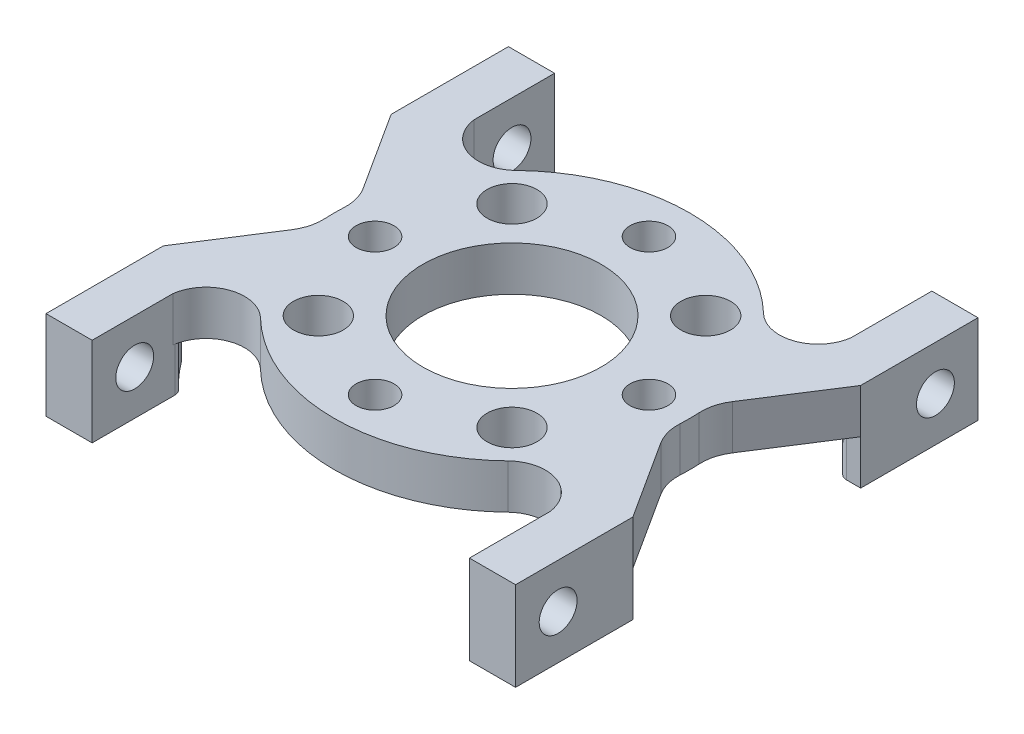
SolidWorks part; units mm, degrees
ref_plane "Front Plane" through (0, 0, 0) normal (0, 0, 1) x (1, 0, 0)
ref_plane "Top Plane" through (0, 0, 0) normal (0, 1, 0) x (1, 0, 0)
ref_plane "Right Plane" through (0, 0, 0) normal (1, 0, 0) x (0, 0, -1)
ref_plane "Plane1" through (0, 0, 0) normal (0, -1, 0) x (1, 0, 0)
sketch "Sketch1" plane through (0, 0, 0) normal (0, -1, 0) x (1, 0, 0)
  line L0 (16.764, 16.51) -> (-16.764, 16.51)
  line L1 (-16.764, 16.51) -> (-16.764, -16.51)
  line L2 (-16.764, -16.51) -> (16.764, -16.51)
  line L3 (16.764, -16.51) -> (16.764, 16.51)
extrude "Boss-Extrude1" add sketch "Sketch1" against normal blind 3.175
sketch "Sketch2" plane through (0, 3.175, 0) normal (0, 1, 0) x (-1, 0, 0)
  line L0 (-13.4696, 16.51) -> (-13.4696, 10.7533)
  line L1 (13.4696, 10.7533) -> (13.4696, 16.51)
  line L2 (13.4696, 16.51) -> (-13.4696, 16.51)
  arc A0 (-13.4696, 10.7533) -> (-8.8308, 9.1273) centre (-10.7425, 11.1033) ccw
  arc A1 (-8.8308, 9.1273) -> (8.8308, 9.1273) centre (0, 0) cw
  arc A2 (8.8308, 9.1273) -> (13.4696, 10.7533) centre (10.7425, 11.1033) ccw
extrude "Cut-Extrude1" cut sketch "Sketch2" against normal through all
sketch "Sketch3" plane through (0, 0, 0) normal (0, -1, 0) x (1, 0, 0)
  line L0 (-13.4696, 8.1331) -> (-16.764, 8.1331)
  line L1 (-16.764, 8.1331) -> (-16.764, 16.51)
  line L2 (-16.764, 16.51) -> (-13.4696, 16.51)
  line L3 (-13.4696, 16.51) -> (-13.4696, 8.1331)
extrude "Boss-Extrude2" add sketch "Sketch3" along normal blind 3.175
sketch "Sketch4" plane through (0, 3.175, 0) normal (0, 1, 0) x (-1, 0, 0)
  line L0 (-16.764, 8.1331) -> (-16.764, -8.1331)
  line L1 (-16.764, -8.1331) -> (-12.5937, -1.6399)
  line L2 (-12.5937, 1.6399) -> (-16.764, 8.1331)
  arc A0 (-12.5937, -1.6399) -> (-12.5937, 1.6399) centre (0, 0) cw
extrude "Cut-Extrude2" cut sketch "Sketch4" against normal through all
sketch "Sketch5" plane through (0, 0, 0) normal (0, -1, 0) x (1, 0, 0)
  line L0 (13.4696, 8.1331) -> (13.4696, 16.51)
  line L1 (13.4696, 16.51) -> (16.764, 16.51)
  line L2 (16.764, 16.51) -> (16.764, 8.1331)
  line L3 (16.764, 8.1331) -> (13.4696, 8.1331)
extrude "Boss-Extrude3" add sketch "Sketch5" along normal blind 3.175
sketch "Sketch6" plane through (0, 3.175, 0) normal (0, 1, 0) x (-1, 0, 0)
  line L0 (13.4696, -16.51) -> (13.4696, -10.7533)
  line L1 (-13.4696, -10.7533) -> (-13.4696, -16.51)
  line L2 (-13.4696, -16.51) -> (13.4696, -16.51)
  arc A0 (13.4696, -10.7533) -> (8.8308, -9.1273) centre (10.7425, -11.1033) ccw
  arc A1 (8.8308, -9.1273) -> (-8.8308, -9.1273) centre (0, 0) cw
  arc A2 (-8.8308, -9.1273) -> (-13.4696, -10.7533) centre (-10.7425, -11.1033) ccw
extrude "Cut-Extrude3" cut sketch "Sketch6" against normal through all
sketch "Sketch7" plane through (0, 0, 0) normal (0, -1, 0) x (1, 0, 0)
  line L0 (13.4696, -8.1331) -> (16.764, -8.1331)
  line L1 (16.764, -8.1331) -> (16.764, -16.51)
  line L2 (16.764, -16.51) -> (13.4696, -16.51)
  line L3 (13.4696, -16.51) -> (13.4696, -8.1331)
extrude "Boss-Extrude4" add sketch "Sketch7" along normal blind 3.175
sketch "Sketch8" plane through (0, 3.175, 0) normal (0, 1, 0) x (-1, 0, 0)
  line L0 (16.764, -8.1331) -> (16.764, 8.1331)
  line L1 (16.764, 8.1331) -> (12.5937, 1.6399)
  line L2 (12.5937, -1.6399) -> (16.764, -8.1331)
  arc A0 (12.5937, 1.6399) -> (12.5937, -1.6399) centre (0, 0) cw
extrude "Cut-Extrude4" cut sketch "Sketch8" against normal through all
sketch "Sketch9" plane through (0, 0, 0) normal (0, -1, 0) x (1, 0, 0)
  line L0 (-13.4696, -8.1331) -> (-13.4696, -16.51)
  line L1 (-13.4696, -16.51) -> (-16.764, -16.51)
  line L2 (-16.764, -16.51) -> (-16.764, -8.1331)
  line L3 (-16.764, -8.1331) -> (-13.4696, -8.1331)
extrude "Boss-Extrude5" add sketch "Sketch9" along normal blind 3.175
sketch "Sketch10" plane through (0, -3.175, 0) normal (0, -1, 0) x (1, 0, 0)
  line L0 (15.4224, -8.1331) -> (13.4696, -8.1331)
  line L1 (13.4696, -8.1331) -> (13.4696, -10.3293)
  arc A0 (13.4696, -10.3293) -> (15.4224, -8.1331) centre (4.064, 0) ccw
extrude "Cut-Extrude5" cut sketch "Sketch10" against normal blind 3.175
sketch "Sketch11" plane through (0, -3.175, 0) normal (0, -1, 0) x (1, 0, 0)
  line L0 (13.4696, 10.3293) -> (13.4696, 8.1331)
  line L1 (13.4696, 8.1331) -> (15.4224, 8.1331)
  arc A0 (15.4224, 8.1331) -> (13.4696, 10.3293) centre (4.064, 0) ccw
extrude "Cut-Extrude6" cut sketch "Sketch11" against normal blind 3.175
sketch "Sketch12" plane through (0, -3.175, 0) normal (0, -1, 0) x (1, 0, 0)
  line L0 (-15.4224, 8.1331) -> (-13.4696, 8.1331)
  line L1 (-13.4696, 8.1331) -> (-13.4696, 10.3293)
  arc A0 (-13.4696, 10.3293) -> (-15.4224, 8.1331) centre (-4.064, 0) ccw
extrude "Cut-Extrude7" cut sketch "Sketch12" against normal blind 3.175
sketch "Sketch13" plane through (0, -3.175, 0) normal (0, -1, 0) x (1, 0, 0)
  line L0 (-13.4696, -10.3293) -> (-13.4696, -8.1331)
  line L1 (-13.4696, -8.1331) -> (-15.4224, -8.1331)
  arc A0 (-15.4224, -8.1331) -> (-13.4696, -10.3293) centre (-4.064, 0) ccw
extrude "Cut-Extrude8" cut sketch "Sketch13" against normal blind 3.175
hole_wizard "Hole1" positions "Sketch15" profile "Sketch14" legacy
sketch "Sketch15" plane through (0, 0, 0) normal (0, -1, 0) x (-1, 0, 0)
  point P0 (0, 0)
sketch "Sketch14" plane through (0, 0, 0) normal (1, 0, 0) x (0, 0, -1)
  line L0 (0, 0) -> (0, 3.175)
  line L1 (0, 3.175) -> (6.3627, 3.175)
  line L2 (6.3627, 3.175) -> (6.3627, 0)
  line L3 (6.3627, 0) -> (0, 0)
  line L4 (0, 110) -> (0, -10) construction
  dimension "Diameter" = 12.7254
  dimension "Depth" = 3.175
hole_wizard "M2.5 Clearance Hole1" positions "Sketch17" profile "Sketch16" hole size "M2.5" standard "ANSI Metric"
sketch "Sketch17" plane through (0, 0, 0) normal (0, -1, 0) x (-1, 0, 0)
  point P0 (0, -9.779)
  point P1 (9.779, 0)
  point P2 (0, 9.779)
  point P3 (-9.779, 0)
sketch "Sketch16" plane through (0, 0, 9.779) normal (1, 0, 0) x (0, 0, -1)
  line L0 (0, 0) -> (0, 3.175)
  line L1 (0, 3.175) -> (1.3525, 3.175)
  line L2 (1.3525, 3.175) -> (1.3525, 0)
  line L5 (1.3525, 0) -> (0, 0)
  line L11 (0, -6.35) -> (0, 107.95) construction
  dimension "Thru Hole Dia." = 2.7051
  dimension "Thru Hole Depth" = 3.175
hole_wizard "M3 Clearance Hole1" positions "Sketch19" profile "Sketch18" hole size "M3" standard "ANSI Metric"
sketch "Sketch19" plane through (0, 0, 0) normal (0, -1, 0) x (-1, 0, 0)
  point P0 (6.9148, -6.9148)
  point P1 (6.9148, 6.9148)
  point P2 (-6.9148, 6.9148)
  point P3 (-6.9148, -6.9148)
sketch "Sketch18" plane through (-6.9148, 0, 6.9148) normal (1, 0, 0) x (0, 0, -1)
  line L0 (0, 0) -> (0, 3.175)
  line L1 (0, 3.175) -> (1.778, 3.175)
  line L2 (1.778, 3.175) -> (1.778, 0)
  line L5 (1.778, 0) -> (0, 0)
  line L11 (0, -6.35) -> (0, 107.95) construction
  dimension "Thru Hole Dia." = 3.556
  dimension "Thru Hole Depth" = 3.175
hole_wizard "M2.5 Clearance Hole2" positions "Sketch21" profile "Sketch20" hole size "M2.5" standard "ANSI Metric"
sketch "Sketch21" plane through (16.764, 0, 0) normal (1, 0, 0) x (0, 0, -1)
  point P0 (13.4704, 0)
sketch "Sketch20" plane through (16.764, 0, -13.4704) normal (0, 1, 0) x (0, 0, -1)
  line L0 (0, 0) -> (0, 3.2944)
  line L1 (0, 3.2944) -> (1.3525, 3.2944)
  line L2 (1.3525, 3.2944) -> (1.3525, 0)
  line L5 (1.3525, 0) -> (0, 0)
  line L11 (0, -6.35) -> (0, 107.95) construction
  dimension "Thru Hole Dia." = 2.7051
  dimension "Thru Hole Depth" = 3.2944
hole_wizard "M2.5 Clearance Hole3" positions "Sketch23" profile "Sketch22" hole size "M2.5" standard "ANSI Metric"
sketch "Sketch23" plane through (13.4696, 0, 0) normal (-1, 0, 0) x (0, 0, 1)
  point P0 (13.4704, 0)
sketch "Sketch22" plane through (13.4696, 0, 13.4704) normal (0, 1, 0) x (0, 0, 1)
  line L0 (0, 0) -> (0, 3.2944)
  line L1 (0, 3.2944) -> (1.3525, 3.2944)
  line L2 (1.3525, 3.2944) -> (1.3525, 0)
  line L5 (1.3525, 0) -> (0, 0)
  line L11 (0, -6.35) -> (0, 107.95) construction
  dimension "Thru Hole Dia." = 2.7051
  dimension "Thru Hole Depth" = 3.2944
hole_wizard "M2.5 Clearance Hole4" positions "Sketch25" profile "Sketch24" hole size "M2.5" standard "ANSI Metric"
sketch "Sketch25" plane through (-13.4696, 0, 0) normal (1, 0, 0) x (0, 0, -1)
  point P0 (-13.4704, 0)
  point P1 (13.4704, 0)
sketch "Sketch24" plane through (-13.4696, 0, 13.4704) normal (0, 1, 0) x (0, 0, -1)
  line L0 (0, 0) -> (0, 3.2944)
  line L1 (0, 3.2944) -> (1.3525, 3.2944)
  line L2 (1.3525, 3.2944) -> (1.3525, 0)
  line L5 (1.3525, 0) -> (0, 0)
  line L11 (0, -6.35) -> (0, 107.95) construction
  dimension "Thru Hole Dia." = 2.7051
  dimension "Thru Hole Depth" = 3.2944
fillet "Fillet1" radius 0.635 8 edges at (-13.4696, -1.5875, -10.3293) (-15.4224, -1.5875, 8.1331) (15.4224, -1.5875, -8.1331) (15.4224, -1.5875, 8.1331) (13.4696, -1.5875, -10.3293) (-13.4696, -1.5875, 10.3293) (-15.4224, -1.5875, -8.1331) (13.4696, -1.5875, 10.3293)
fillet "Fillet2" radius 3.175 4 edges at (-12.5937, 1.5875, -1.6399) (12.5937, 1.5875, -1.6399) (-12.5937, 1.5875, 1.6399) (12.5937, 1.5875, 1.6399)
